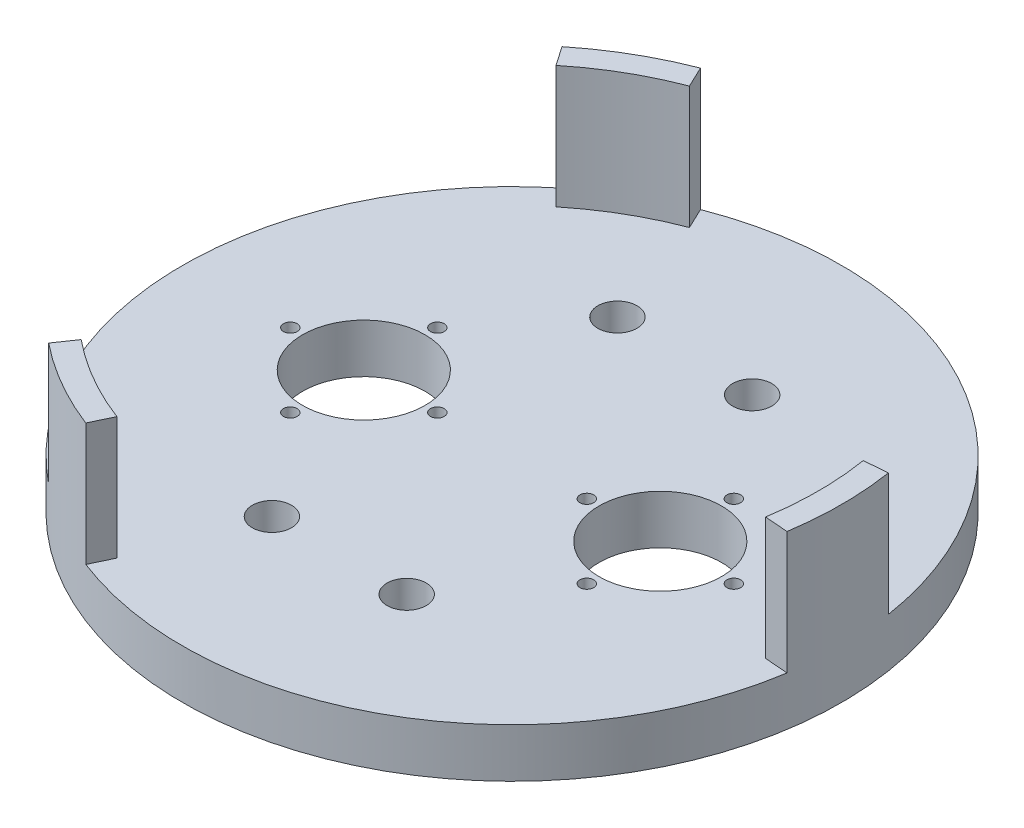
SolidWorks part; units mm, degrees
material "6061-T6 (SS)"
ref_plane "Front" through (0, 0, 0) normal (0, 0, 1) x (1, 0, 0)
ref_plane "Top" through (0, 0, 0) normal (0, 1, 0) x (1, 0, 0)
ref_plane "Right" through (0, 0, 0) normal (1, 0, 0) x (0, 0, -1)
sketch "Sketch1" plane through (0, 0, 0) normal (0, 1, 0) x (1, 0, 0)
  line L1 (0, 0) -> (127.635, 0)
  line L2 (0, 0) -> (0, 127.635)
  line L3 (0, 127.635) -> (127.635, 127.635)
  line L4 (127.635, 0) -> (127.635, 127.635)
  dimension "D1" = 127.635
  dimension "D2" = 127.635
extrude "Main Plate" add sketch "Sketch1" along normal blind 12.7
sketch "Sketch9" plane through (0, 12.7, 0) normal (0, 1, 0) x (1, 0, 0)
  circle A0 centre (63.8175, 63.8175) radius 85.725
  dimension "D1" = 171.45
extrude "Boss-Extrude1" add sketch "Sketch9" against normal up to surface (12.7 mm away) contours A0 up to face at (63.8175, 0, -63.8175)
sketch "Sketch10" plane through (0, 12.7, 0) normal (0, 1, 0) x (1, 0, 0)
  circle A0 centre (63.8175, 63.8175) radius 95.25
  circle A1 centre (63.8175, 63.8175) radius 85.4075
  dimension "D1" = 170.815
  dimension "D2" = 190.5
extrude "Cut-Extrude1" cut sketch "Sketch10" against normal blind 167.64 contours A0 | A1
sketch "Sketch14" plane through (0, 12.7, 0) normal (0, 1, 0) x (1, 0, 0)
  line L0 (201.1692, 63.8175) -> (-73.4523, 63.8175) construction
ref_plane "Plane1" through (0, 0, -63.8175) normal (0, 0, -1) x (-1, 0, 0)
ref_plane "Plane3" through (0, 6.35, 0) normal (0, 1, 0) x (1, 0, 0)
ref_plane "Plane2" through (-21.59, 0, 0) normal (-1, 0, 0) x (0, 0, 1)
sketch "Sketch18" plane through (0, 6.35, 0) normal (0, 1, 0) x (1, 0, 0)
  circle A0 centre (63.8175, 63.8175) radius 85.4075
  circle A1 centre (63.8175, 63.8175) radius 79.375
  circle A4 centre (63.8175, 63.8175) radius 85.4075 construction
  dimension "D1" = 158.75
extrude "Boss-Extrude2" add sketch "Sketch18" along normal blind 38.1
sketch "Sketch20" plane through (0, 12.7, 0) normal (0, 1, 0) x (1, 0, 0)
  line L0 (63.8175, 143.1925) -> (63.8175, -15.5575) construction
  line L1 (-15.5575, 63.8175) -> (143.1925, 63.8175) construction
  line L2 (63.8175, 63.8175) -> (-15.5575, -73.664) construction
  circle A0 centre (63.8175, 63.8175) radius 79.375 construction
  dimension "D1" = 30
ref_plane "Plane5" through (-15.5575, 12.7, 73.664) normal (-0.5, 0, 0.866) x (0.866, 0, 0.5)
sketch "Sketch15" plane through (166.2216, 0, 178.6143) normal (0.5, 0, -0.866) x (-0.866, 0, -0.5)
  line L3 (289.2754, 44.45) -> (130.5254, 44.45) construction
  line L4 (124.4929, 0) -> (295.3079, 0) construction
  line L6 (278.6412, 12.7) -> (141.1597, 12.7) construction
  circle A0 centre (209.9004, 22.225) radius 2.159
  circle A1 centre (209.9004, 38.1) radius 2.159
  circle A2 centre (209.9004, 6.35) radius 2.159
  point P16 (209.9004, 12.7)
  dimension "D1" = 4.318
  dimension "D2" = 15.875
  dimension "D3" = 4.318
  dimension "D4" = 4.318
  dimension "D5" = 6.35
  dimension "D6" = 6.35
  dimension "D7" = 0
extrude "Cut-Extrude3" [suppressed] cut sketch "Sketch15" along normal blind 88.9
pattern_circular "CirPattern1" [suppressed] count 3 over 360
ref_plane "Plane4" through (63.8175, 0, 0) normal (-1, 0, 0) x (0, 0, 1)
sketch "Sketch21" plane through (0, 12.7, 0) normal (0, 1, 0) x (1, 0, 0)
  line L1 (-15.5575, 63.8175) -> (143.1925, 63.8175) construction
  line L2 (102.235, 63.8175) -> (102.235, 100.651) construction
  line L3 (63.8175, 87.3125) -> (63.8175, -87.3125) construction
  circle A0 centre (102.235, 63.8175) radius 15.875
  circle A1 centre (102.235, 82.8675) radius 1.778
  circle A2 centre (25.4, 63.8175) radius 15.875
  circle A3 centre (121.285, 63.8175) radius 1.778
  circle A4 centre (102.235, 44.7675) radius 1.778
  circle A5 centre (83.185, 63.8175) radius 1.778
  circle A6 centre (25.4, 82.8675) radius 1.778
  circle A7 centre (6.35, 63.8175) radius 1.778
  circle A8 centre (25.4, 44.7675) radius 1.778
  circle A9 centre (44.45, 63.8175) radius 1.778
  dimension "D1" = 31.75
  dimension "D2" = 3.556
  dimension "D6" = 19.05
  dimension "D3" = 19.05
  dimension "D4" = 76.835
  dimension "D7" = 19.05
  dimension "D5" = 4
extrude "CO2 Mounts" cut sketch "Sketch21" against normal through all
sketch "Sketch22" plane through (0, 12.7, 0) normal (0, 1, 0) x (1, 0, 0)
  line L0 (63.8175, 87.3125) -> (63.8175, -87.3125) construction
  line L1 (87.3125, 63.8175) -> (-87.3125, 63.8175) construction
  circle A0 centre (46.355, 108.585) radius 5.08
  circle A1 centre (81.28, 108.585) radius 5.08
  circle A2 centre (81.28, 19.05) radius 5.08
  circle A3 centre (46.355, 19.05) radius 5.08
  dimension "D1" = 10.16
  dimension "D2" = 34.925
  dimension "D3" = 89.535
extrude "Cut-Extrude5" cut sketch "Sketch22" against normal through all
sketch "Sketch23" plane through (0, 12.7, 0) normal (0, 1, 0) x (1, 0, 0)
  line L0 (13.6787, 125.352) -> (7.5523, 134.2379)
  line L1 (15.1867, 11.8815) -> (13.6787, 2.283) construction
  line L3 (-15.5575, 63.8175) -> (143.1925, 63.8175) construction
  line L4 (63.8175, 143.1925) -> (63.8175, -15.5575) construction
  line L5 (-15.5575, 63.8175) -> (143.1925, 63.8175)
  line L6 (63.8175, 143.1925) -> (63.8175, -15.5575)
  line L7 (13.6787, 2.283) -> (6.9592, -7.4631)
  line L8 (-19.2671, 125.3206) -> (-48.797, 60.3978)
  line L9 (-48.797, 60.3978) -> (-9.8843, 7.0525)
  line L10 (-9.8843, 7.0525) -> (6.9592, -7.4631)
  line L11 (24.1345, -4.9259) -> (13.6787, 2.283) construction
  line L14 (7.5523, 134.2379) -> (-19.2671, 125.3206)
  line L15 (24.1345, 132.5609) -> (13.6787, 125.352) construction
  line L28 (63.8175, 63.8175) -> (24.1345, -4.9259) construction
  line L29 (63.8175, 63.8175) -> (24.1345, 132.5609) construction
  line L30 (142.1773, 76.4717) -> (152.9359, 77.3344)
  line L31 (152.9359, 77.3344) -> (158.6231, 105.0193)
  line L32 (158.6231, 105.0193) -> (117.1632, 163.0543)
  line L33 (117.1632, 163.0543) -> (51.5085, 156.0277)
  line L34 (51.5085, 156.0277) -> (30.5159, 148.6985)
  line L35 (35.5964, 138.0062) -> (30.5159, 148.6985)
  line L36 (35.5964, -10.3712) -> (30.9643, -20.1198)
  line L37 (30.9643, -20.1198) -> (52.0965, -38.8874)
  line L38 (52.0965, -38.8874) -> (123.0863, -31.9996)
  line L39 (123.0863, -31.9996) -> (149.8284, 28.3723)
  line L40 (149.8284, 28.3723) -> (153.9775, 50.217)
  line L41 (142.1773, 51.1633) -> (153.9775, 50.217)
  circle A0 centre (63.8175, 63.8175) radius 79.375 construction
  arc A1 (13.6787, 2.283) -> (13.6787, 125.352) centre (63.8175, 63.8175) cw
  circle A3 centre (63.8175, 63.8175) radius 79.375
  arc A6 (35.5964, 138.0062) -> (142.1773, 76.4717) centre (63.8175, 63.8175) cw
  arc A7 (142.1773, 51.1633) -> (35.5964, -10.3712) centre (63.8175, 63.8175) cw
  circle A9 centre (63.8175, 63.8175) radius 79.375
  dimension "D1" = 79.375
  dimension "D2" = 0
  dimension "D3" = 12.7
  dimension "D4" = 90
  dimension "D5" = 12.7
  dimension "D6" = 90
  dimension "D8" = 60.004
  dimension "D9" = 60.004
  dimension "D7" = 3
extrude "Cut-Extrude6" cut sketch "Sketch23" along normal blind 111.6
